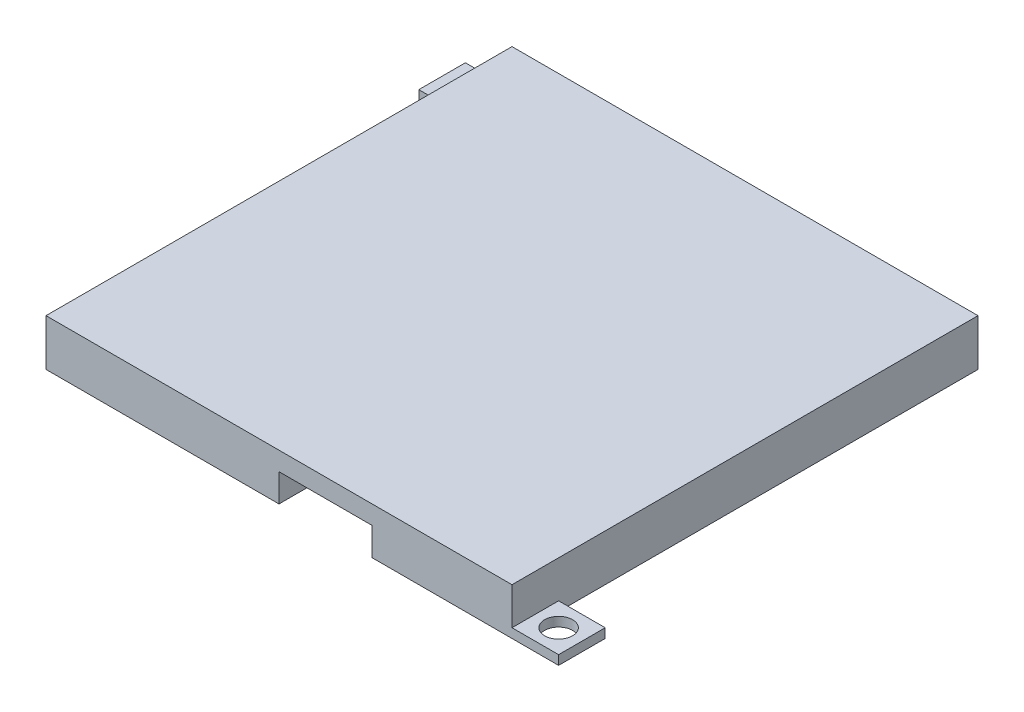
SolidWorks part; units mm, degrees
ref_plane "Front Plane" through (0, 0, 0) normal (0, 0, 1) x (1, 0, 0)
ref_plane "Top Plane" through (0, 0, 0) normal (0, 1, 0) x (1, 0, 0)
ref_plane "Right Plane" through (0, 0, 0) normal (1, 0, 0) x (0, 0, -1)
sketch "Sketch1" plane through (0, 0, 0) normal (0, 1, 0) x (1, 0, 0)
  line L0 (25, -25) -> (-25, -25)
  line L1 (25, -25) -> (25, 25)
  line L2 (-25, -25) -> (-25, 25)
  line L3 (25, 25) -> (-25, 25)
  line L4 (25, -25) -> (-25, 25) construction
  line L5 (-25, -25) -> (25, 25) construction
  point P1 (0, 0)
  dimension "D1" = 50
  dimension "D2" = 50
extrude "Boss-Extrude2" add sketch "Sketch1" along normal blind 5
sketch "Sketch2" plane through (0, 0, 0) normal (0, -1, 0) x (-1, 0, 0)
  line L0 (-20, -20) -> (20, -20)
  line L1 (-20, -20) -> (-20, 20)
  line L2 (20, -20) -> (20, 20)
  line L3 (-20, 20) -> (20, 20)
  line L4 (-20, -20) -> (20, 20) construction
  line L5 (20, -20) -> (-20, 20) construction
  point P1 (0, 0)
  dimension "D1" = 40
  dimension "D2" = 40
extrude "Cut-Extrude1" cut sketch "Sketch2" against normal blind 3
sketch "Sketch3" plane through (0, 0, 0) normal (0, -1, 0) x (-1, 0, 0)
  line L0 (25, 25) -> (30, 25)
  line L1 (30, 25) -> (30, 20)
  line L2 (30, 20) -> (25, 20)
  line L3 (25, 25) -> (25, -25) construction
  line L4 (25, 20) -> (25, 25)
  line L5 (-25, -25) -> (-30, -25)
  line L6 (-30, -25) -> (-30, -20)
  line L7 (-30, -20) -> (-25, -20)
  line L8 (-25, -25) -> (-25, 25) construction
  line L9 (-25, -20) -> (-25, -25)
  dimension "D1" = 5
  dimension "D2" = 5
  dimension "D3" = 5
  dimension "D4" = 5
extrude "Boss-Extrude3" add sketch "Sketch3" against normal blind 1
sketch "Sketch4" plane through (0, 1, 0) normal (0, 1, 0) x (1, 0, 0)
  circle A0 centre (-27.5, 22.5) radius 1.5
  circle A1 centre (27.5, -22.5) radius 1.5
  dimension "D1" = 3
  dimension "D2" = 3
extrude "Cut-Extrude2" cut sketch "Sketch4" against normal blind 1
ref_plane "Plane1" through (0, 0, 25) normal (0, 0, 1) x (1, 0, 0)
sketch "Sketch6" plane through (0, 0, 25) normal (0, 0, 1) x (1, 0, 0)
  line L0 (0, 0) -> (10, 0)
  line L1 (-25, 0) -> (30, 0) construction
  line L2 (0, 0) -> (0, 3)
  line L3 (0, 3) -> (10, 3)
  line L4 (10, 3) -> (10, 0)
  dimension "D1" = 3
  dimension "D2" = 10
extrude "Cut-Extrude3" cut sketch "Sketch6" against normal blind 10
